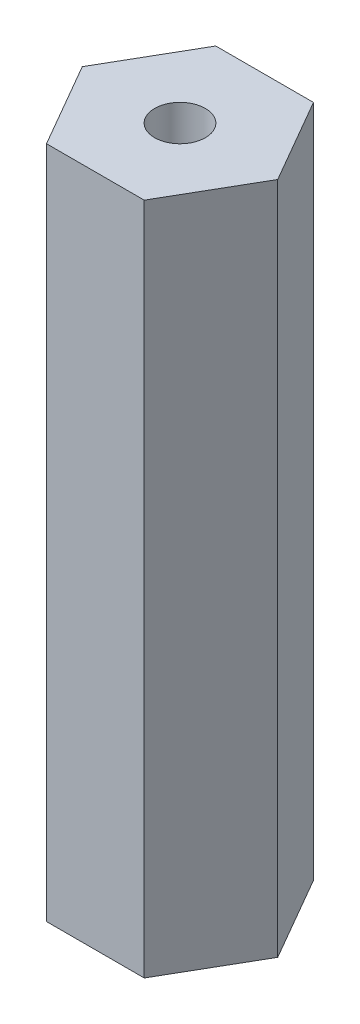
SolidWorks part; units mm, degrees
ref_plane "Спереди" through (0, 0, 0) normal (0, 0, 1) x (1, 0, 0)
ref_plane "Сверху" through (0, 0, 0) normal (0, 1, 0) x (1, 0, 0)
ref_plane "Справа" through (0, 0, 0) normal (1, 0, 0) x (0, 0, -1)
sketch "Эскиз1" plane through (0, 0, 0) normal (0, 1, 0) x (1, 0, 0)
  line L1 (2.8868, 0) -> (1.4434, 2.5)
  line L2 (1.4434, 2.5) -> (-1.4434, 2.5)
  line L3 (-1.4434, 2.5) -> (-2.8868, 0)
  line L4 (-2.8868, 0) -> (-1.4434, -2.5)
  line L5 (-1.4434, -2.5) -> (1.4434, -2.5)
  line L6 (1.4434, -2.5) -> (2.8868, 0)
  circle A0 centre (0, 0) radius 2.5 construction
  dimension "D1" = 5
extrude "Бобышка-Вытянуть1" add sketch "Эскиз1" against normal up to surface (19.9 mm away) from surface
sketch "Эскиз2" plane through (0, 30.7, 0) normal (0, 1, 0) x (1, 0, 0)
  circle A0 centre (0, 0) radius 0.75
  dimension "D1" = 1.5
extrude "Вырез-Вытянуть1" cut sketch "Эскиз2" against normal through all
